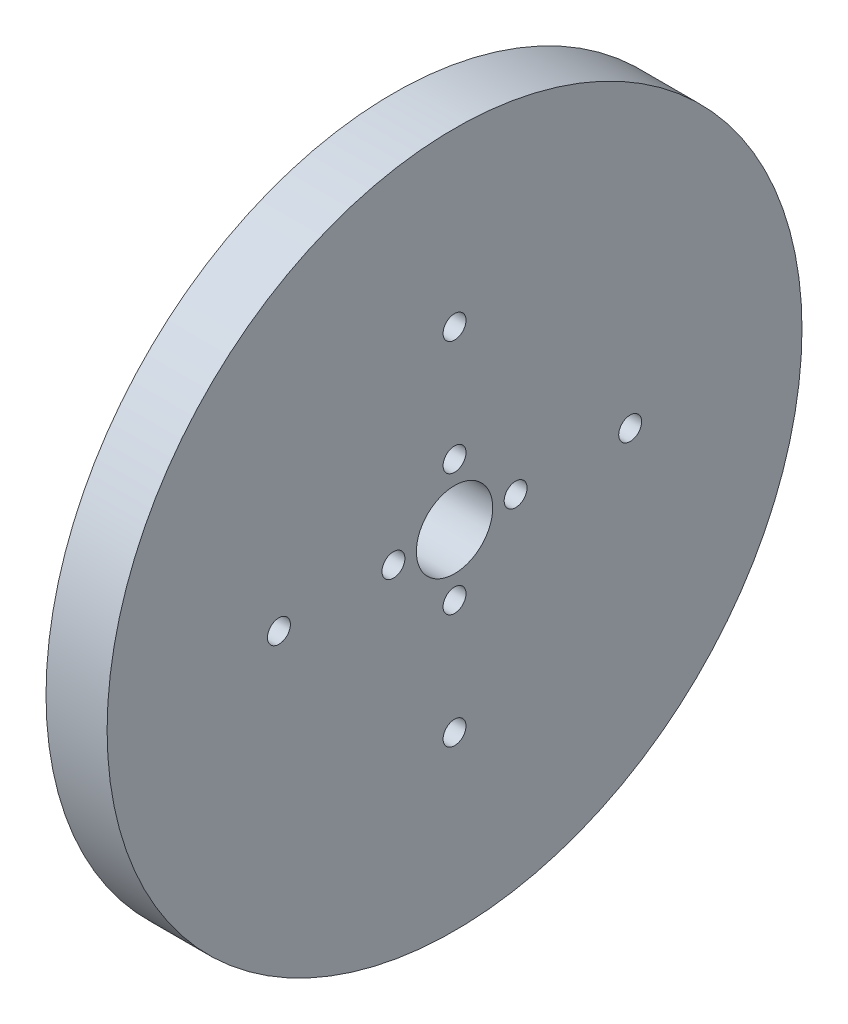
SolidWorks part; units mm, degrees
material "PMMA"
ref_plane "Front Plane" through (0, 0, 0) normal (0, 0, 1) x (1, 0, 0)
ref_plane "Top Plane" through (0, 0, 0) normal (0, 1, 0) x (1, 0, 0)
ref_plane "Right Plane" through (0, 0, 0) normal (1, 0, 0) x (0, 0, -1)
sketch "Sprocket" plane through (0, 0, 0) normal (1, 0, 0) x (0, 0, -1)
  circle A0 centre (0, 0) radius 45.5
  dimension "D1" = 91
extrude "Estrusione-Estrusione2" add sketch "Sprocket" along normal blind 8 contours A0
sketch "Schizzo1" plane through (0, 0, 0) normal (1, 0, 0) x (0, 0, -1)
  line L0 (0, 45.5) -> (0, -45.5) construction
  line L4 (-45.5, 0) -> (45.5, 0) construction
  circle A0 centre (0, 0) radius 5
  circle A1 centre (0, 23) radius 1.5
  circle A2 centre (8, 0) radius 1.5
  circle A3 centre (0, 8) radius 1.5
  circle A4 centre (23, 0) radius 1.5
  circle A5 centre (0, -8) radius 1.5
  circle A6 centre (0, -23) radius 1.5
  circle A7 centre (0, 0) radius 45.5 construction
  circle A8 centre (-8, 0) radius 1.5
  circle A9 centre (-23, 0) radius 1.5
  circle A10 centre (5.6569, 5.6569) radius 1.5 [skipped]
  circle A11 centre (-5.6569, 5.6569) radius 1.5 [skipped]
  circle A12 centre (-5.6569, -5.6569) radius 1.5 [skipped]
  circle A13 centre (5.6569, -5.6569) radius 1.5 [skipped]
  point P5 (0, 0)
  point P8 (0, 0)
  point P30 (0, 0)
  point P39 (0, 0)
  dimension "D1" = 10
  dimension "D2" = 3
  dimension "D5" = 3
  dimension "D3" = 8
  dimension "D6" = 15
  dimension "D4" = 8
  dimension "D7" = 4
extrude "Taglio-Estrusione2" cut sketch "Schizzo1" along direction (1, 0, 0) on the side of the normal through all
sketch "Schizzo2" plane through (0, 0, 0) normal (1, 0, 0) x (0, 0, -1)
  line L0 (0, 4) -> (0, 5) construction
  line L1 (3.9686, -0.5) -> (4.9749, -0.5)
  line L2 (-0.5, 4.9749) -> (-0.5, 3.9686)
  line L3 (0.5, 3.9686) -> (0.5, 4.9749)
  line L4 (4.9749, 0.5) -> (3.9686, 0.5)
  line L5 (-0.5, -3.9686) -> (-0.5, -4.9749)
  line L6 (0.5, -4.9749) -> (0.5, -3.9686)
  line L7 (-3.9686, 0.5) -> (-4.9749, 0.5)
  line L8 (-4.9749, -0.5) -> (-3.9686, -0.5)
  circle A0 centre (0, 0) radius 2
  circle A1 centre (0, 0) radius 4
  arc A3 (-0.5, 4.9749) -> (0.5, 4.9749) centre (0, 0) cw
  arc A4 (-0.5, 3.9686) -> (0.5, 3.9686) centre (0, 0) cw
  arc A5 (4.9749, 0.5) -> (4.9749, -0.5) centre (0, 0) cw
  arc A6 (3.9686, 0.5) -> (3.9686, -0.5) centre (0, 0) cw
  arc A7 (0.5, -4.9749) -> (-0.5, -4.9749) centre (0, 0) cw
  arc A8 (0.5, -3.9686) -> (-0.5, -3.9686) centre (0, 0) cw
  arc A9 (-4.9749, -0.5) -> (-4.9749, 0.5) centre (0, 0) cw
  arc A10 (-3.9686, -0.5) -> (-3.9686, 0.5) centre (0, 0) cw
  point P30 (0, 0)
  dimension "D1" = 4
  dimension "D2" = 8
  dimension "D3" = 0.5
  dimension "D5" = 4
  dimension "D4" = 0.5
extrude "Estrusione-Estrusione3" [suppressed] add sketch "Schizzo2" along normal blind 8 contours A1 A4 A0 | A9 L8 A1 L7 | A7 L6 A1 L5 | A5 L4 A1 L1
equation "\"Thickness8\"=8"
equation "\"D1@Estrusione-Estrusione2\"=\"Thickness8\""
equation "\"D\"=91"
equation "\"D1@Sprocket\"=\"D\""
equation "\"D4@Schizzo1\"=\"D3@Schizzo1\""
equation "\"D1@Estrusione-Estrusione3\"=\"Thickness8\""
